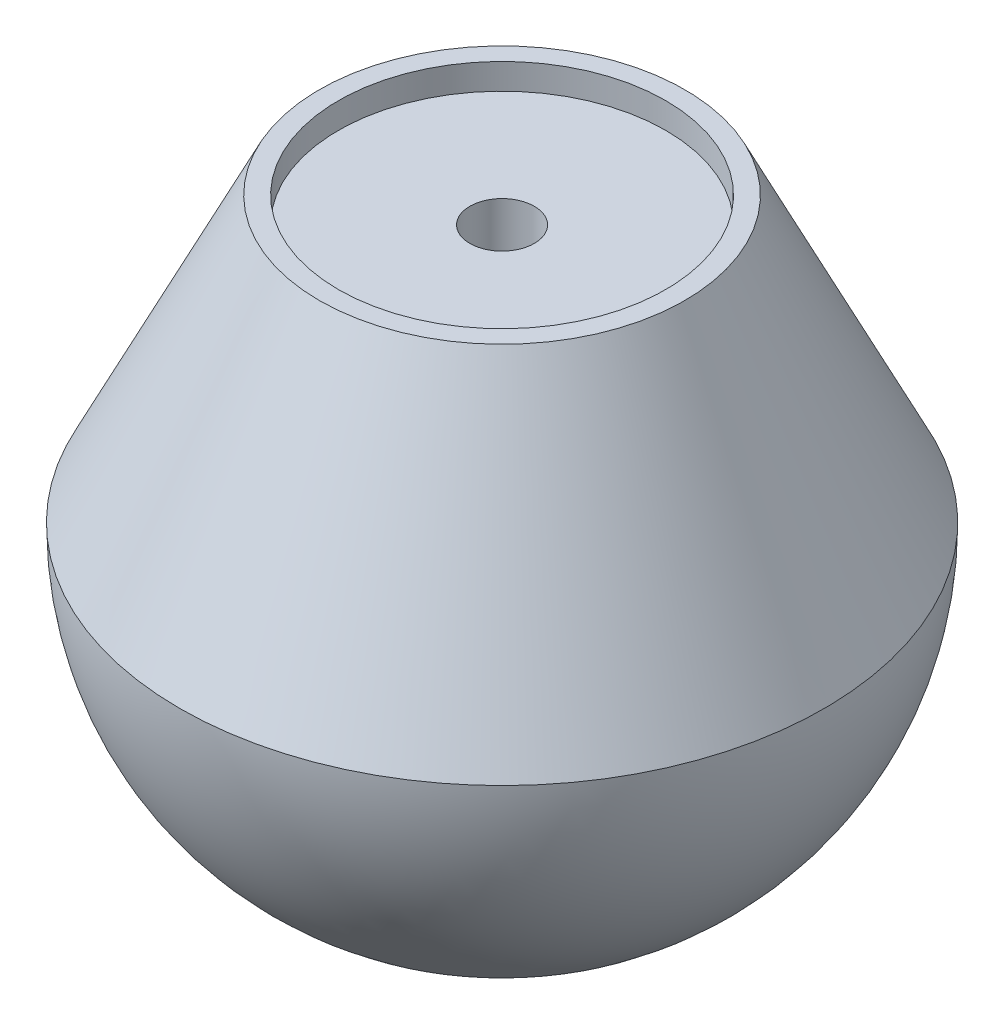
SolidWorks part; units mm, degrees
ref_plane "Front Plane" through (0, 0, 0) normal (0, 0, 1) x (1, 0, 0)
ref_plane "Top Plane" through (0, 0, 0) normal (0, 1, 0) x (1, 0, 0)
ref_plane "Right Plane" through (0, 0, 0) normal (1, 0, 0) x (0, 0, -1)
other "Configuration Table"
sketch "Sketch1" plane through (0, 0, 0) normal (0, 0, 1) x (1, 0, 0)
  line L0 (0, 0) -> (0, -25) construction
  line L1 (0, 0) -> (0, 25) construction
  line L2 (0, 25) -> (-12.7, 25) construction
  line L3 (0, 25) -> (12.7, 25) construction
  line L4 (0, 0) -> (-25, 0) construction
  line L5 (0, 0) -> (25, 0) construction
  line L6 (-14.176, 22) -> (-25, 0)
  line L7 (14.176, 22) -> (25, 0)
  line L8 (-12.7, 22) -> (-12.7, 20)
  line L9 (-12.7, 20) -> (-2.5, 20)
  line L10 (12.7, 20) -> (12.7, 22)
  line L11 (-2.5, 20) -> (-2.5, 0)
  line L12 (2.5, 20) -> (2.5, -0.0042)
  line L13 (-2.5, 20) -> (0, 20) construction
  line L14 (2.5, 20) -> (12.7, 20)
  line L15 (0, 20) -> (2.5, 20) construction
  line L16 (-2.5, 0) -> (-5, 0)
  line L17 (-5, 0) -> (-5, -22)
  line L18 (2.5, -0.0042) -> (5, -0.0042)
  line L19 (5, -0.0042) -> (5, -22)
  line L20 (0, 22) -> (-12.7, 22) construction
  line L21 (0, 22) -> (12.7, 22) construction
  line L22 (-12.7, 22) -> (-14.176, 22)
  line L23 (12.7, 22) -> (14.176, 22)
  line L24 (-12.7, 25) -> (-14.176, 22) construction
  line L25 (-12.7, 25) -> (-12.7, 22) construction
  line L26 (12.7, 22) -> (12.7, 25) construction
  line L27 (12.7, 25) -> (14.176, 22) construction
  line L28 (-5, -22) -> (-11.8743, -22)
  line L29 (5, -22) -> (11.8743, -22)
  line L30 (-5, -22) -> (-5, -24.4949) construction
  line L31 (5, -22) -> (5, -24.4949) construction
  line L32 (0, -22) -> (-5, -22) construction
  line L33 (0, -22) -> (5, -22) construction
  arc A0 (-25, 0) -> (-11.8743, -22) centre (0, 0) ccw
  arc A1 (0, -25) -> (5, -24.4949) centre (0, 0) ccw construction
  arc A2 (11.8743, -22) -> (25, 0) centre (0, 0) ccw
  arc A3 (-5, -24.4949) -> (0, -25) centre (0, 0) ccw construction
  arc A4 (-11.8743, -22) -> (-5, -24.4949) centre (0, 0) ccw construction
  arc A5 (5, -24.4949) -> (11.8743, -22) centre (0, 0) ccw construction
  dimension "D4" = 5
  dimension "D1" = 25
  dimension "D2" = 25.4
  dimension "D3" = 3
  dimension "D5" = 20
  dimension "D6" = 20.0042
  dimension "D7" = 2.5
  dimension "D8" = 5
  dimension "D9" = 3
revolve "Revolve1" add sketch "Sketch1" angle 360 about L0
fillet "Fillet1" radius 0.5 2 edges at (0, -22, 11.8743) (0, -22, 5)
